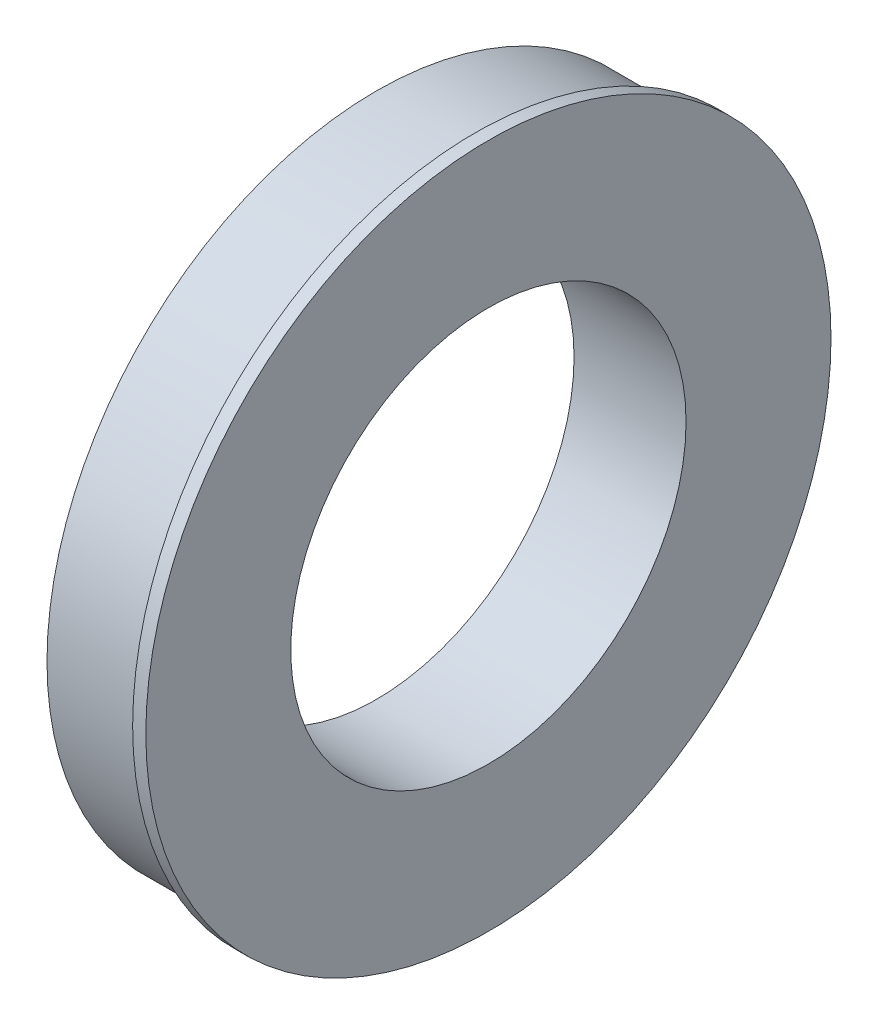
SolidWorks part; units mm, degrees
material "Aluminum Bronze"
ref_plane "Front Plane" through (0, 0, 0) normal (0, 0, 1) x (1, 0, 0)
ref_plane "Top Plane" through (0, 0, 0) normal (0, 1, 0) x (1, 0, 0)
ref_plane "Right Plane" through (0, 0, 0) normal (1, 0, 0) x (0, 0, -1)
sketch "Sketch1" plane through (0, 0, 0) normal (1, 0, 0) x (0, 0, -1)
  circle A0 centre (0, 0) radius 63.5
  circle A1 centre (0, 0) radius 38.1
  dimension "D1" = 127
  dimension "D2" = 76.2
extrude "Boss-Extrude1" add sketch "Sketch1" along normal blind 19.05
sketch "Sketch2" plane through (19.05, 0, 0) normal (1, 0, 0) x (0, 0, -1)
  circle A1 centre (0, 0) radius 38.1 construction
  circle A2 centre (0, 0) radius 66.04
  circle A3 centre (0, 0) radius 66.04
  circle A4 centre (0, 0) radius 38.1
  dimension "D1" = 2.54
extrude "Boss-Extrude2" add sketch "Sketch2" along normal blind 2.54
